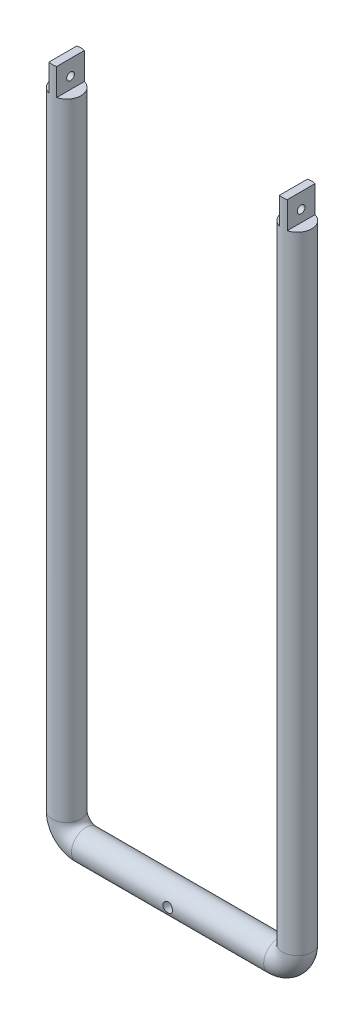
SolidWorks part; units mm, degrees
ref_plane "Front Plane" through (0, 0, 0) normal (0, 0, 1) x (1, 0, 0)
ref_plane "Top Plane" through (0, 0, 0) normal (0, 1, 0) x (1, 0, 0)
ref_plane "Right Plane" through (0, 0, 0) normal (1, 0, 0) x (0, 0, -1)
sketch "Sketch1" plane through (0, 0, 0) normal (0, 0, 1) x (1, 0, 0)
  line L0 (-67, 350) -> (47, 350) construction
  line L1 (-60, 350) -> (-60, 10)
  line L2 (-50, 0) -> (50, 0)
  line L3 (60, 10) -> (60, 350)
  line L4 (0, 0) -> (0, 303.2062) construction
  arc A2 (-50, 0) -> (-60, 10) centre (-50, 10) cw
  arc A3 (50, 0) -> (60, 10) centre (50, 10) ccw
  dimension "D1" = 100
  dimension "D3" = 10
  dimension "D4" = 10
  dimension "D5" = 340
  dimension "D6" = 60
  dimension "D7" = 60
  dimension "D8" = 0
sweep "Sweep2" add path "Sketch1" circular profile diameter 15 parameters "D3"=15
sketch "Sketch40" plane through (0, 0, 0) normal (1, 0, 0) x (0, 0, -1)
  line L0 (7.5, 350) -> (-7.5, 350) construction
  line L1 (7.5, 350) -> (-5, 350) construction
  circle A0 centre (0, 342) radius 2
  dimension "D1" = 4
  dimension "D2" = 8
sketch "Sketch41" plane through (0, 0, 0) normal (0, 0, 1) x (1, 0, 0)
  line L0 (-67.5, 350) -> (-67.5, 336)
  line L1 (-67.5, 350) -> (-67.5, 10) construction
  line L2 (-67.5, 336) -> (-62, 336)
  line L3 (-62, 336) -> (-62, 350)
  line L4 (-52.5, 350) -> (-67.5, 350) construction
  line L5 (-62, 350) -> (-67.5, 350)
  line L6 (-52.5, 350) -> (-52.5, 336)
  line L7 (-52.5, 10) -> (-52.5, 350) construction
  line L8 (-52.5, 336) -> (-58, 336)
  line L9 (-58, 336) -> (-58, 350)
  line L10 (-58, 350) -> (-52.5, 350)
  line L11 (0, 173.4406) -> (0, 362.5632) construction
  line L12 (58, 350) -> (52.5, 350)
  line L13 (52.5, 350) -> (52.5, 336)
  line L14 (52.5, 336) -> (58, 336)
  line L15 (58, 336) -> (58, 350)
  line L16 (62, 336) -> (62, 350)
  line L17 (67.5, 336) -> (62, 336)
  line L18 (62, 350) -> (67.5, 350)
  line L19 (67.5, 350) -> (67.5, 336)
  point P14 (-55.25, 350)
  point P20 (55.25, 350)
  dimension "D1" = 14
  dimension "D2" = 5.5
  dimension "D3" = 14
  dimension "D4" = 5.5
extrude "Cut-Extrude1" cut sketch "Sketch41" against normal mid plane 15
extrude "Cut-Extrude2" cut sketch "Sketch40" against normal mid plane 130 contours A0
sketch "Sketch42" plane through (0, 0, 0) normal (0, 0, 1) x (1, 0, 0)
  circle A0 centre (0, 0) radius 2.5
  dimension "D1" = 5
extrude "Cut-Extrude3" cut sketch "Sketch42" against normal mid plane 20
